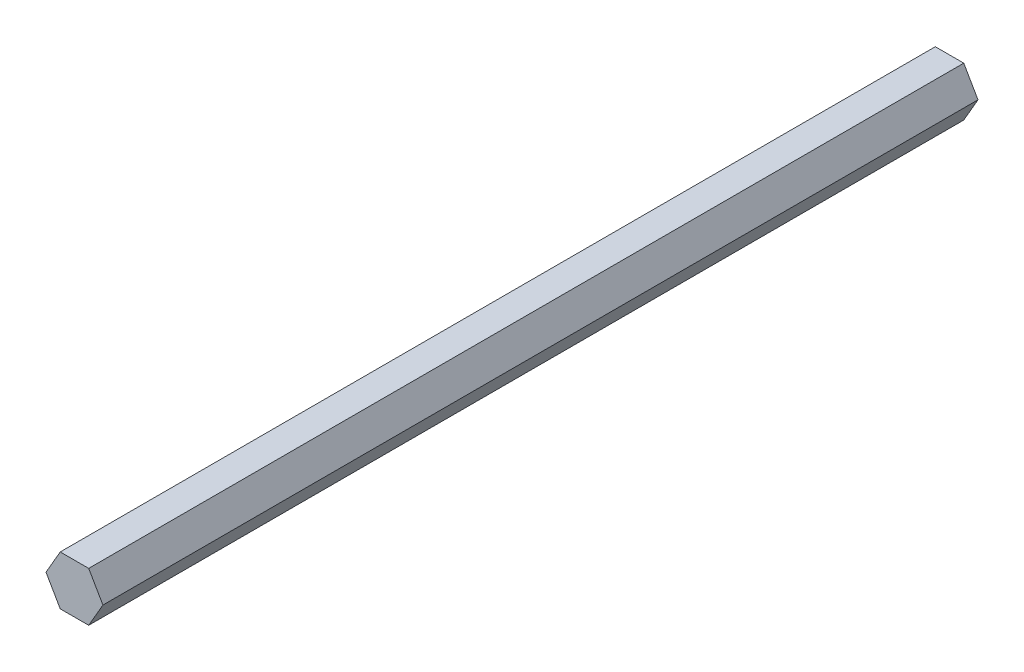
SolidWorks part; units mm, degrees
ref_plane "Front Plane" through (0, 0, 0) normal (0, 0, 1) x (1, 0, 0)
ref_plane "Top Plane" through (0, 0, 0) normal (0, 1, 0) x (1, 0, 0)
ref_plane "Right Plane" through (0, 0, 0) normal (1, 0, 0) x (0, 0, -1)
sketch "Sketch1" plane through (0, 0, 0) normal (0, 0, 1) x (1, 0, 0)
  line L1 (-7.3323, 0) -> (-3.6662, -6.35)
  line L2 (-3.6662, -6.35) -> (3.6662, -6.35)
  line L3 (3.6662, -6.35) -> (7.3323, 0)
  line L4 (7.3323, 0) -> (3.6662, 6.35)
  line L5 (3.6662, 6.35) -> (-3.6662, 6.35)
  line L6 (-3.6662, 6.35) -> (-7.3323, 0)
  circle A0 centre (0, 0) radius 6.35 construction
  dimension "D1" = 12.7
extrude "Boss-Extrude1" add sketch "Sketch1" along normal blind 225.425
